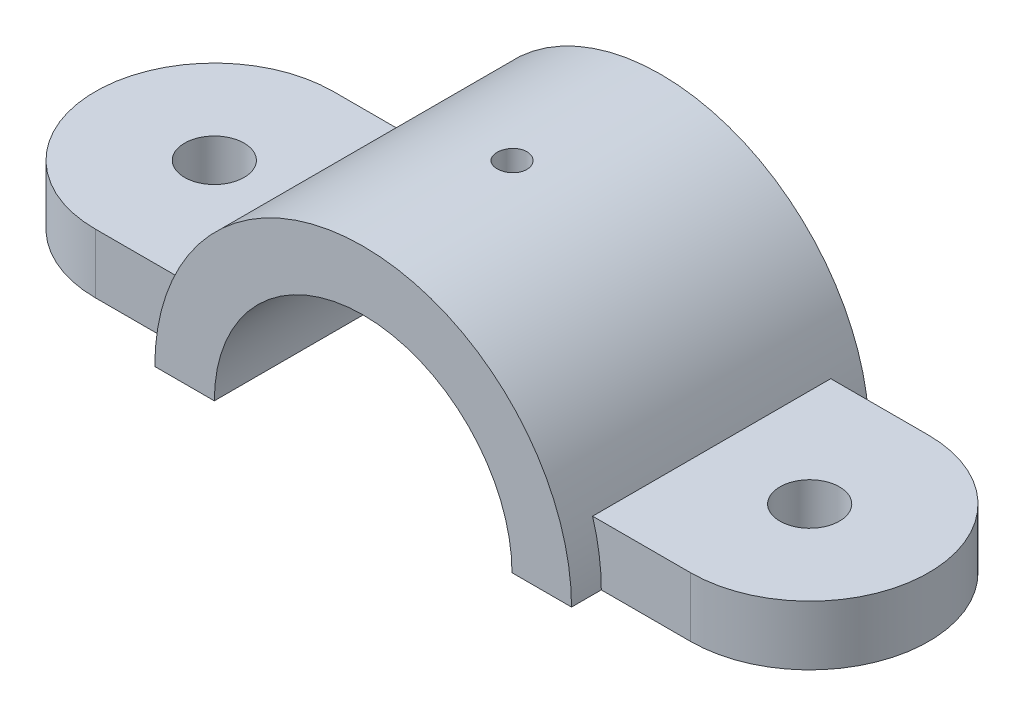
SolidWorks part; units mm, degrees
ref_plane "Front Plane" through (0, 0, 0) normal (0, 0, 1) x (1, 0, 0)
ref_plane "Top Plane" through (0, 0, 0) normal (0, 1, 0) x (1, 0, 0)
ref_plane "Right Plane" through (0, 0, 0) normal (1, 0, 0) x (0, 0, -1)
sketch "slotSketch" plane through (0, 0, 0) normal (0, 1, 0) x (1, 0, 0)
  line L0 (-63.5, 0) -> (63.5, 0) construction
  line L1 (-63.5, 25.4) -> (63.5, 25.4)
  line L2 (-63.5, -25.4) -> (63.5, -25.4)
  line L3 (0, 0) -> (0, 43.3751) construction
  arc A0 (-63.5, 25.4) -> (-63.5, -25.4) centre (-63.5, 0) ccw
  arc A1 (63.5, -25.4) -> (63.5, 25.4) centre (63.5, 0) ccw
  circle A2 centre (63.5, 0) radius 6.35
  circle A3 centre (-63.5, 0) radius 6.35
  point P3 (0, 0)
  dimension "D2" = 25.4
  dimension "D3" = 12.7
  dimension "D1" = 127
extrude "slotExtrude" add sketch "slotSketch" along normal blind 12.7
sketch "Sketch3" plane through (0, 0, 0) normal (0, 0, 1) x (1, 0, 0)
  line L0 (-63.5, 0) -> (63.5, 0) construction
  line L5 (-63.5, 0) -> (63.5, 0)
  line L6 (63.5, 0) -> (63.5, 12.7)
  line L7 (63.5, 12.7) -> (-63.5, 12.7)
  line L8 (-63.5, 12.7) -> (-63.5, 0)
  line L9 (-44.45, 0) -> (44.45, 0)
  arc A0 (-44.45, 0) -> (44.45, 0) centre (0, 0) cw
  dimension "D1" = 44.45
  dimension "D2" = 0
extrude "arcExtrude" add sketch "Sketch3" along normal mid plane 63.5
sketch "Sketch4" plane through (0, 0, 31.75) normal (0, 0, 1) x (1, 0, 0)
  line L0 (-44.45, 0) -> (44.45, 0) construction
  line L1 (-25.4, 19.05) -> (25.4, 19.05)
  line L2 (-25.4, 19.05) -> (-25.4, 0)
  line L3 (-25.4, 0) -> (25.4, 0)
  line L4 (25.4, 19.05) -> (25.4, 0)
  point P6 (0, 0)
  point P9 (0, 0)
  dimension "D1" = 19.05
  dimension "D2" = 50.8
extrude "squareProfile" [suppressed] cut sketch "Sketch4" against normal through all
hole_wizard "centerDrill" positions "Sketch5" profile "Sketch6" hole size "#97" standard "ANSI Inch" end condition through all
sketch "Sketch5" plane through (0, 0, 0) normal (0, -1, 0) x (-1, 0, 0)
  point P0 (0, 0)
sketch "Sketch6" plane through (0, 0, 0) normal (1, 0, 0) x (0, 0, -1)
  line L0 (0, 0) -> (0, 44.45)
  line L1 (0, 44.45) -> (3.175, 44.45)
  line L2 (3.175, 44.45) -> (3.175, 0)
  line L5 (3.175, 0) -> (0, 0)
  line L11 (0, -6.35) -> (0, 107.95) construction
  dimension "Thru Hole Dia." = 6.35
  dimension "Thru Hole Depth" = 44.45
sketch "Sketch7" plane through (0, 0, 31.75) normal (0, 0, 1) x (1, 0, 0)
  line L0 (-44.45, 0) -> (44.45, 0) construction
  line L1 (-31.75, 0) -> (31.75, 0)
  arc A0 (-31.75, 0) -> (31.75, 0) centre (0, 0) cw
  dimension "D1" = 63.5
extrude "arcProfile" cut sketch "Sketch7" against normal through all
equation "\"slotLength\"= 5"
equation "\"slotHole\"= .5"
equation "\"slotRad\"= 1"
equation "\"slotHeight\"= .5"
equation "\"D1@slotSketch\"= \"slotLength\""
equation "\"D2@slotSketch\"= \"slotRad\""
equation "\"D1@slotExtrude\"= \"slotHeight\""
equation "\"D3@slotSketch\"= \"slotHole\""
equation "\"arcRad\"= 1.75"
equation "\"arcExtrude\"= 2.5"
equation "\"D1@Sketch3\"=\"arcRad\""
equation "\"D1@arcExtrude\" = \"arcExtrude\""
